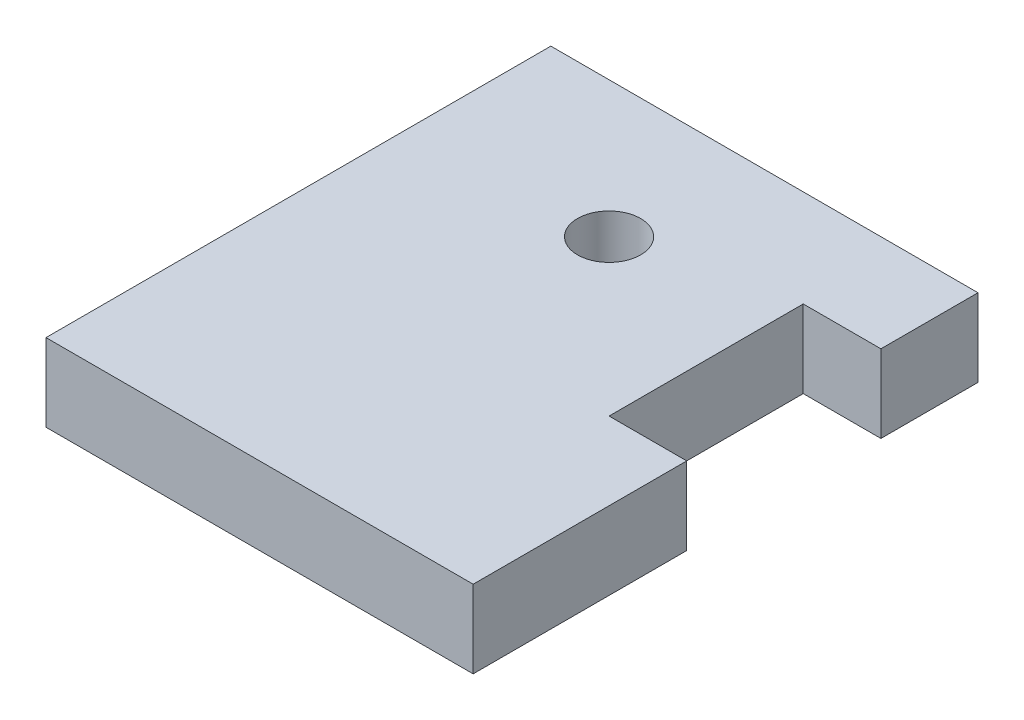
SolidWorks part; units mm, degrees
ref_plane "Front Plane" through (0, 0, 0) normal (0, 0, 1) x (1, 0, 0)
ref_plane "Top Plane" through (0, 0, 0) normal (0, 1, 0) x (1, 0, 0)
ref_plane "Right Plane" through (0, 0, 0) normal (1, 0, 0) x (0, 0, -1)
sketch "Sketch1" plane through (0, 0, 0) normal (0, 1, 0) x (1, 0, 0)
  line L9 (0, 0) -> (22, 0)
  line L17 (0, 0) -> (0, 26)
  line L18 (0, 26) -> (22, 26)
  line L19 (22, 0) -> (22, 11)
  line L20 (22, 21) -> (18, 21)
  line L22 (22, 11) -> (18, 11)
  line L23 (18, 21) -> (18, 11)
  line L24 (22, 21) -> (22, 26)
  circle A1 centre (10, 19) radius 1.625
  dimension "D6" = 7
  dimension "D7" = 3.25
  dimension "D1" = 26
  dimension "D2" = 22
  dimension "D3" = 4
  dimension "D4" = 5
  dimension "D5" = 10
  dimension "D8" = 10
extrude "Boss-Extrude1" add sketch "Sketch1" along normal blind 4
